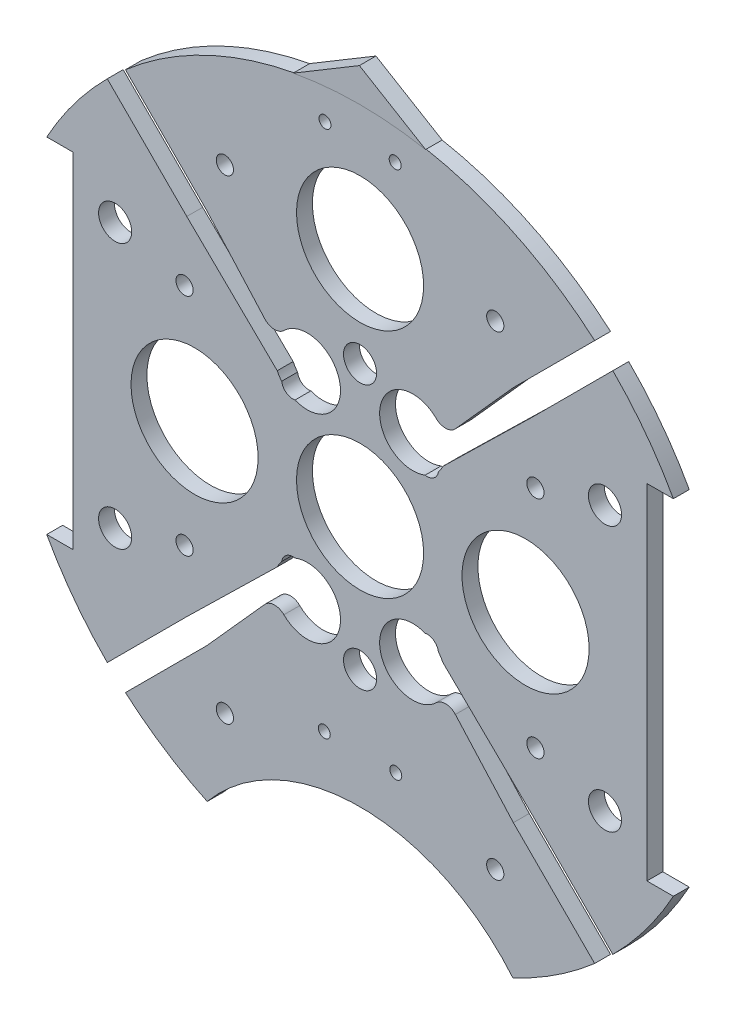
SolidWorks part; units mm, degrees
ref_plane "Front Plane" through (0, 0, 0) normal (0, 0, 1) x (1, 0, 0)
ref_plane "Top Plane" through (0, 0, 0) normal (0, 1, 0) x (1, 0, 0)
ref_plane "Right Plane" through (0, 0, 0) normal (1, 0, 0) x (0, 0, -1)
sketch "Sketch1" plane through (0, 0, 0) normal (0, 0, 1) x (1, 0, 0)
  line L0 (0, 0) -> (-82.1241, 0) construction
  line L1 (0, 0) -> (0, 95.6219) construction
  line L3 (-60.1074, 33.02) -> (-55.0274, 33.02)
  line L5 (-60.1074, -33.02) -> (-55.0274, -33.02)
  line L6 (-55.0274, 33.02) -> (-55.0274, -33.02)
  line L7 (60.1074, -33.02) -> (55.0274, -33.02)
  line L8 (60.1074, 33.02) -> (55.0274, 33.02)
  line L9 (55.0274, 33.02) -> (55.0274, -33.02)
  arc A0 (-60.1074, -33.02) -> (60.1074, -33.02) centre (0, 0) ccw
  circle A1 centre (-46.482, 10.795) radius 1.651 construction
  circle A2 centre (-21.082, 10.795) radius 1.651 construction
  circle A3 centre (-21.082, -10.795) radius 1.651 construction
  circle A4 centre (-46.482, -10.795) radius 1.651 construction
  circle A5 centre (46.482, -10.795) radius 1.651 construction
  circle A6 centre (21.082, -10.795) radius 1.651 construction
  circle A7 centre (21.082, 10.795) radius 1.651 construction
  circle A8 centre (46.482, 10.795) radius 1.651 construction
  arc A9 (60.1074, 33.02) -> (-60.1074, 33.02) centre (0, 0) ccw
  dimension "D2" = 3.302
  dimension "D3" = 3.302
  dimension "D4" = 25.4
  dimension "D5" = 10.795
  dimension "D10" = 46.482
  dimension "D12" = 10.795
  dimension "D6" = 66.04
  dimension "D7" = 5.08
  dimension "D8" = 68.58
  dimension "D9" = 68.58
  dimension "D11" = 33.02
extrude "Boss-Extrude2" add sketch "Sketch1" along normal blind 3.048
sketch "Sketch4" plane through (0, 0, 0) normal (0, 0, -1) x (-1, 0, 0)
  line L0 (0, 0) -> (0, -122.8047) construction
  line L1 (33.02, -67.2621) -> (-33.02, -67.2621)
  arc A0 (-60.1074, -33.02) -> (60.1074, -33.02) centre (0, 0) ccw construction
  circle A1 centre (0, -86.3121) radius 38.1
  dimension "D4" = 76.2
  dimension "D5" = 0
  dimension "D6" = 19.05
  dimension "D1" = 74.93
  dimension "D2" = 74.93
  dimension "D3" = 66.04
extrude "Cut-Extrude3" cut sketch "Sketch4" against normal through all
sketch "Sketch9" plane through (0, 0, 0) normal (0, 0, -1) x (-1, 0, 0)
  line L0 (12.7, 67.3938) -> (0, 75)
  line L1 (0, 75) -> (-12.7, 67.3938)
  arc A2 (12.7, 67.3938) -> (-12.7, 67.3938) centre (0, 0) ccw
extrude "Boss-Extrude3" add sketch "Sketch9" against normal blind 3.175
extrude "Cut-Extrude7" cut sketch "Sketch10" against normal through all
sketch "Sketch10" plane through (-31.3134, 132.559, 6.35) normal (0, 0, 1) x (0, 1, 0)
  line L0 (-132.559, -31.3134) -> (-245.9178, -31.3134) construction
  line L1 (-132.559, -31.3134) -> (-132.559, -129.4011) construction
  circle A0 centre (-180.819, -4.6434) radius 1.651
  circle A3 centre (-180.819, -57.9834) radius 1.651
  circle A4 centre (-84.299, -57.9834) radius 1.651
  circle A5 centre (-84.299, -4.6434) radius 1.651
extrude "Cut-Extrude8" cut sketch "Sketch11" against normal through all both and the other way through all
sketch "Sketch11" plane through (-31.3134, 132.614, 38.1) normal (0, 0, 1) x (0, 1, 0)
  line L0 (-132.614, -31.3134) -> (-132.614, 57.8454) construction
  line L1 (-132.614, -31.3134) -> (-222.516, -31.3134) construction
  circle A0 centre (-158.014, 14.4066) radius 3.175
  circle A1 centre (-173.254, -31.3134) radius 3.175
  circle A3 centre (-158.014, -77.0334) radius 3.175
  circle A4 centre (-107.214, -77.0334) radius 3.175
  circle A5 centre (-91.974, -31.3134) radius 3.175
  circle A6 centre (-107.214, 14.4066) radius 3.175
sketch "Sketch12" plane through (0, 0, 0) normal (0, 0, -1) x (-1, 0, 0)
  line L0 (0, -13.969) -> (0, 24.0636) construction
  circle A0 centre (6.731, 62.23) radius 1.143
  circle A1 centre (-6.731, 62.23) radius 1.143
  dimension "D1" = 2.286
  dimension "D2" = 62.23
  dimension "D3" = 6.731
extrude "Cut-Extrude9" cut sketch "Sketch12" against normal through all
extrude "Cut-Extrude12" cut sketch "Sketch15" against normal blind 75.692
sketch "Sketch15" plane through (30.092, 4.0835, -3.048) normal (0, 0, -1) x (-1, 0, 0)
  circle A0 centre (63.7572, 17.5065) radius 1.651
  circle A1 centre (63.7572, -25.6735) radius 1.651
  circle A2 centre (-3.5528, -25.6735) radius 1.651
  circle A3 centre (-3.5528, 17.5065) radius 1.651
extrude "Cut-Extrude14" cut sketch "Sketch17" against normal blind 97.79
sketch "Sketch17" plane through (30.092, 4.0835, -33.0835) normal (0, 0, -1) x (-1, 0, 0)
  line L0 (30.092, -29.4835) -> (30.092, 6.2385) construction
  circle A0 centre (4.1544, -49.7288) radius 1.651
  circle A4 centre (56.0296, -49.7288) radius 1.651
  circle A5 centre (4.1544, 41.3825) radius 1.651
  circle A9 centre (56.0296, 41.3825) radius 1.651
sketch "Sketch18" plane through (0, 0, 0) normal (0, 0, -1) x (-1, 0, 0)
  line L0 (0, 0) -> (0, -37.9941) construction
  circle A0 centre (31.75, 0) radius 12.192
  circle A1 centre (-31.75, 0) radius 12.192
  dimension "D1" = 24.384
  dimension "D2" = 31.75
extrude "Cut-Extrude15" cut sketch "Sketch18" against normal blind 35.56
extrude "Cut-Extrude16" cut sketch "Sketch19" against normal blind 48.768 and the other way blind 103.378
sketch "Sketch19" plane through (30.092, 4.0835, 3.048) normal (0, 0, -1) x (-1, 0, 0)
  line L0 (30.092, -4.0835) -> (148.6336, -4.0835) construction
  line L1 (30.092, -4.0835) -> (30.092, 90.452) construction
  circle A0 centre (-16.898, 21.3165) radius 3.175
  circle A1 centre (77.082, 21.3165) radius 3.175
  circle A2 centre (30.092, 21.3165) radius 3.175
  circle A4 centre (77.082, -29.4835) radius 3.175
  circle A5 centre (30.092, -29.4835) radius 3.175
  circle A6 centre (-16.898, -29.4835) radius 3.175
sketch "Sketch5" plane through (0, 0, 0) normal (0, 0, -1) x (-1, 0, 0)
  line L0 (45.1258, 51.861) -> (11.5228, 18.258) construction
  line L1 (-69.4248, 0) -> (69.4248, 0) construction
  line L2 (48.4934, -48.4934) -> (33.2448, -33.2448)
  line L3 (15.8876, 16.2964) -> (33.2448, 33.2448)
  line L4 (29.4103, -36.1455) -> (45.1258, -51.861)
  line L5 (45.1258, -51.861) -> (48.4934, -48.4934)
  line L6 (-15.2664, -15.2664) -> (-65.8076, -65.8076) construction
  line L7 (15.5824, -17.3784) -> (-2.7323, 0.9363) construction
  line L8 (16.1122, 21.3038) -> (29.4103, 36.1455)
  line L9 (-48.4934, 48.4934) -> (-6.6635, 6.6635) construction
  line L10 (-16.1122, 21.3038) -> (-29.4103, 36.1455)
  line L11 (48.4934, 48.4934) -> (15.2664, 15.2664) construction
  line L12 (-15.8876, 16.2964) -> (-33.2448, 33.2448)
  line L13 (0, 0) -> (46.9211, -12.5725) construction
  line L14 (29.4103, -36.1455) -> (16.1122, -21.3038)
  line L15 (-45.1258, 51.861) -> (-11.6404, 18.1832) construction
  line L16 (-45.1258, -51.861) -> (-13.0585, -19.7937) construction
  line L17 (45.1258, -51.861) -> (17.3018, -24.037) construction
  line L18 (0, 0) -> (-46.9211, -12.5725) construction
  line L19 (0, 0) -> (-0.898, -0.898) construction
  line L20 (33.2448, -33.2448) -> (15.8876, -16.2964)
  line L21 (4.9069, -1.3148) -> (-4.984, 8.5761) construction
  line L22 (-29.4103, -36.1455) -> (-16.1122, -21.3038)
  line L23 (-33.2448, -33.2448) -> (-15.8876, -16.2964)
  line L27 (-45.1258, -51.861) -> (-48.4934, -48.4934)
  line L28 (-29.4103, -36.1455) -> (-45.1258, -51.861)
  line L30 (0, 58.5122) -> (0, -56.1975) construction
  line L31 (-48.4934, -48.4934) -> (-33.2448, -33.2448)
  line L34 (-48.4934, 48.4934) -> (-33.2448, 33.2448)
  line L36 (-29.4103, 36.1455) -> (-45.1258, 51.861)
  line L37 (-45.1258, 51.861) -> (-48.4934, 48.4934)
  line L43 (15.2664, -15.2664) -> (65.8076, -65.8076) construction
  line L47 (0, 6.7352) -> (-14.4605, -7.7253) construction
  line L53 (45.1258, 51.861) -> (48.4934, 48.4934)
  line L54 (29.4103, 36.1455) -> (45.1258, 51.861)
  line L56 (48.4934, 48.4934) -> (33.2448, 33.2448)
  circle A0 centre (0, 0) radius 21.59 construction
  arc A1 (29.3285, -61.9924) -> (60.1074, -33.02) centre (0, 0) ccw construction
  arc A2 (12.4846, -13.1281) -> (15.0363, -14.9737) centre (12.8656, -15.2882) cw
  arc A3 (15.0363, 14.9737) -> (12.4846, 13.1281) centre (12.8656, 15.2882) cw
  arc A4 (-12.4846, 13.1281) -> (-15.0363, 14.9737) centre (-12.8656, 15.2882) cw
  arc A5 (-12.4846, -13.1281) -> (-15.0363, -14.9737) centre (-12.8656, -15.2882) ccw
  arc A6 (15.0363, 14.9737) -> (15.8876, 16.2964) centre (10.1352, 19.0632) ccw
  arc A7 (-15.0363, 14.9737) -> (-15.8876, 16.2964) centre (-10.1352, 19.0632) cw
  arc A8 (-15.0363, -14.9737) -> (-15.8876, -16.2964) centre (-10.1352, -19.0632) ccw
  arc A9 (15.0363, -14.9737) -> (15.8876, -16.2964) centre (10.1352, -19.0632) cw
  arc A10 (16.1122, 21.3038) -> (12.4846, 13.1281) centre (10.1352, 19.0632) ccw
  arc A11 (-16.1122, 21.3038) -> (-12.4846, 13.1281) centre (-10.1352, 19.0632) cw
  arc A12 (16.1122, -21.3038) -> (12.4846, -13.1281) centre (10.1352, -19.0632) cw
  arc A13 (-16.1122, -21.3038) -> (-12.4846, -13.1281) centre (-10.1352, -19.0632) ccw
  circle A14 centre (0, 0) radius 12.192
  circle A15 centre (0, 44.45) radius 12.192
  dimension "D7" = 44.45
  dimension "D6" = 43.18
  dimension "D5" = 24.384
  dimension "D1" = 12.7663
  dimension "D4" = 24.384
  dimension "D2" = 4.7625
  dimension "D3" = 22.225
  dimension "D9" = 15
extrude "Cut-Extrude6" cut sketch "Sketch5" against normal through all
fillet "Fillet1" radius 2.54 4 edges at (-16.1122, -21.3038, 1.524) (16.1122, -21.3038, 1.524) (16.1122, 21.3038, 1.524) (-16.1122, 21.3038, 1.524)
sketch "Sketch20" plane through (0, 0, 0) normal (0, 0, -1) x (-1, 0, 0)
  circle A0 centre (-6.858, -39.116) radius 1.143
  circle A1 centre (6.858, -39.116) radius 1.143
  circle A2 centre (-6.731, 62.23) radius 1.143 construction
  point P6 (0, 0)
  point P7 (0, 0)
  dimension "D1" = 0
  dimension "D2" = 13.716
  dimension "D3" = 6.858
  dimension "D4" = 39.116
extrude "Cut-Extrude17" cut sketch "Sketch20" against normal through all
